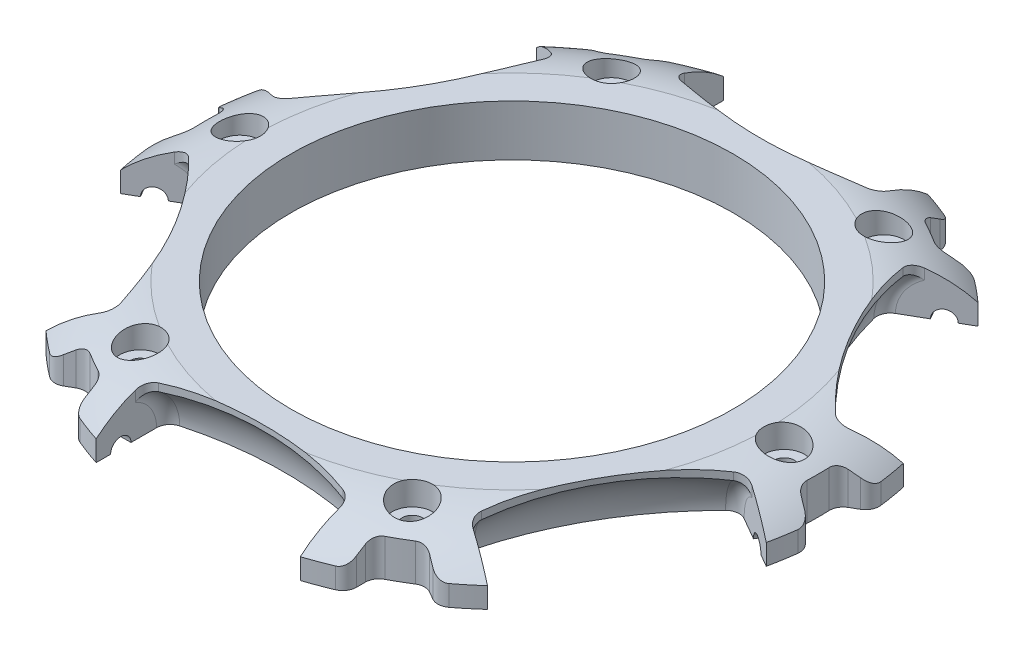
SolidWorks part; units mm, degrees
ref_plane "Front Plane" through (0, 0, 0) normal (0, 0, 1) x (1, 0, 0)
ref_plane "Top Plane" through (0, 0, 0) normal (0, 1, 0) x (1, 0, 0)
ref_plane "Right Plane" through (0, 0, 0) normal (1, 0, 0) x (0, 0, -1)
sketch "Sketch1" plane through (0, 0, 0) normal (0, 1, 0) x (1, 0, 0)
  line L10 (0, 0) -> (0, -50) construction
  line L11 (15, -42.5) -> (-15, -42.5) construction
  line L12 (15, -37.303) -> (15, -47.697)
  line L13 (-15, -37.303) -> (-15, -47.697)
  line L14 (-24.8054, -31.6419) -> (-33.8068, -36.8389)
  line L15 (-39.8054, -5.6611) -> (-48.8068, -10.8581)
  line L16 (-29.3061, -34.2404) -> (-44.3061, -8.2596) construction
  line L17 (-39.8054, 5.6611) -> (-48.8068, 10.8581)
  line L18 (-24.8054, 31.6419) -> (-33.8068, 36.8389)
  line L19 (-44.3061, 8.2596) -> (-29.3061, 34.2404) construction
  line L20 (-15, 37.303) -> (-15, 47.697)
  line L21 (15, 37.303) -> (15, 47.697)
  line L22 (-15, 42.5) -> (15, 42.5) construction
  line L23 (24.8054, 31.6419) -> (33.8068, 36.8389)
  line L24 (39.8054, 5.6611) -> (48.8068, 10.8581)
  line L25 (29.3061, 34.2404) -> (44.3061, 8.2596) construction
  line L26 (39.8054, -5.6611) -> (48.8068, -10.8581)
  line L27 (24.8054, -31.6419) -> (33.8068, -36.8389)
  line L28 (44.3061, -8.2596) -> (29.3061, -34.2404) construction
  line L103 (-16.5, -36.2148) -> (-16.5, -47.697)
  line L104 (16.5, -36.2148) -> (16.5, -47.697)
  circle A3 centre (0, 0) radius 50
  circle A4 centre (0, 0) radius 42.5 construction
  arc A8 (-15, -37.303) -> (15, -37.303) centre (0, -85) cw
  arc A9 (-39.8054, -5.6611) -> (-24.8054, -31.6419) centre (-73.6122, -42.5) cw
  arc A10 (-24.8054, 31.6419) -> (-39.8054, 5.6611) centre (-73.6122, 42.5) cw
  arc A11 (15, 37.303) -> (-15, 37.303) centre (0, 85) cw
  arc A12 (39.8054, 5.6611) -> (24.8054, 31.6419) centre (73.6122, 42.5) cw
  arc A13 (24.8054, -31.6419) -> (39.8054, -5.6611) centre (73.6122, -42.5) cw
  circle A38 centre (0, 0) radius 33.5
  circle A39 centre (0, 0) radius 28
  arc A40 (-16.5, -36.2148) -> (16.5, -36.2148) centre (0, -85) cw
  circle A41 centre (0, 0) radius 31
  point P18 (0, -42.5)
  point P28 (-36.8061, -21.25)
  point P36 (-36.8061, 21.25)
  point P44 (0, 42.5)
  point P52 (36.8061, 21.25)
  point P60 (36.8061, -21.25)
  point P65 (0, 0)
  dimension "D1" = 30
  dimension "D2" = 100
  dimension "D3" = 85
  dimension "D4" = 6
  dimension "D5" = 1.5
  dimension "D6" = 2.5
  dimension "D7" = 3
sketch "Sketch2" plane through (0, 0, 0) normal (0, 1, 0) x (1, 0, 0)
  circle A0 centre (0, 0) radius 50 construction
  circle A1 centre (0, 0) radius 50
extrude "Boss-Extrude1" add sketch "Sketch2" along normal blind 7.5
sketch "Sketch3" plane through (0, 0, 0) normal (0, 1, 0) x (1, 0, 0)
  line L5 (-20.18, -42.5) -> (20.5663, -42.5) construction
  line L6 (-15, -42.5) -> (15, -42.5)
  line L7 (-15, -42.5) -> (-15, -35.7329)
  line L8 (15, -42.5) -> (15, -35.7329)
  arc A0 (16.5, -36.2148) -> (-16.5, -36.2148) centre (0, -85) ccw construction
  arc A1 (15, -35.7329) -> (-15, -35.7329) centre (0, -85) ccw
revolve "Cut-Revolve1" cut sketch "Sketch3" angle 360 about L5
sketch "Sketch4" plane through (0, 0, 0) normal (0, 1, 0) x (1, 0, 0)
  line L5 (15, -38.8779) -> (15, -47.697)
  line L6 (-15, -37.303) -> (-15, -47.697) construction
  line L7 (-15, -38.8779) -> (-15, -47.697)
  arc A0 (16.5, -36.2148) -> (-16.5, -36.2148) centre (0, -85) ccw construction
  arc A1 (16.5, -36.2148) -> (-16.5, -36.2148) centre (0, -85) ccw construction
  arc A2 (15, -38.8779) -> (-15, -38.8779) centre (0, -85) ccw
  circle A3 centre (0, 0) radius 50 construction
  arc A4 (-15, -47.697) -> (15, -47.697) centre (0, 0) ccw
  dimension "D1" = 3
extrude "Cut-Extrude2" cut sketch "Sketch4" along normal up to next (7.5 mm away)
sketch "Sketch5" plane through (0, 0, 0) normal (1, 0, 0) x (0, 0, -1)
  circle A0 centre (-42.5, 0) radius 1.5
  point P0 (-42.5, 0)
  dimension "D1" = 3
extrude "Cut-Extrude3" cut sketch "Sketch5" against normal blind 18 and the other way blind 18
pattern_circular "CirPattern1" count 6 over 360 about axis through (0, 0, 0) along (0, 1, 0) of "Cut-Revolve1", "Cut-Extrude2", "Cut-Extrude3"
sketch "Sketch6" plane through (0, 0, 0) normal (0, -1, 0) x (1, 0, 0)
  line L0 (-29.1051, 37.5885) -> (-26.507, 36.0885) construction
  line L1 (-18, 44) -> (-18, 41) construction
  line L2 (-29.1051, 37.5885) -> (-26.507, 36.0885) construction
  line L3 (-18, 44) -> (-18, 41) construction
  line L4 (-20, 44) -> (-20, 41) construction
  line L5 (-28.1051, 39.3205) -> (-25.507, 37.8205) construction
  line L6 (-28.2647, 39.4126) -> (-24.9106, 37.4762)
  line L7 (-20, 40.3113) -> (-20, 44.1843)
  line L8 (20, 44.1843) -> (20, 40.3113)
  line L9 (24.9106, 37.4762) -> (28.2647, 39.4126)
  line L10 (48.2647, 4.7716) -> (44.9106, 2.8351)
  line L11 (44.9106, -2.8351) -> (48.2647, -4.7716)
  line L12 (28.2647, -39.4126) -> (24.9106, -37.4762)
  line L13 (20, -40.3113) -> (20, -44.1843)
  line L14 (-20, -44.1843) -> (-20, -40.3113)
  line L15 (-24.9106, -37.4762) -> (-28.2647, -39.4126)
  line L16 (-48.2647, -4.7716) -> (-44.9106, -2.8351)
  line L17 (-44.9106, 2.8351) -> (-48.2647, 4.7716)
  circle A1 centre (0, 0) radius 50 construction
  arc A4 (-20, 40.3113) -> (-24.9106, 37.4762) centre (0, 0) ccw
  arc A5 (-28.2647, 39.4126) -> (-48.2647, 4.7716) centre (0, 0) ccw
  arc A6 (24.9106, 37.4762) -> (20, 40.3113) centre (0, 0) ccw
  circle A7 centre (0, 0) radius 50
  arc A10 (44.9106, -2.8351) -> (44.9106, 2.8351) centre (0, 0) ccw
  arc A12 (20, -40.3113) -> (24.9106, -37.4762) centre (0, 0) ccw
  arc A14 (-24.9106, -37.4762) -> (-20, -40.3113) centre (0, 0) ccw
  arc A16 (-44.9106, 2.8351) -> (-44.9106, -2.8351) centre (0, 0) ccw
  arc A18 (20, 44.1843) -> (-20, 44.1843) centre (0, 0) ccw
  arc A19 (48.2647, 4.7716) -> (28.2647, 39.4126) centre (0, 0) ccw
  arc A20 (28.2647, -39.4126) -> (48.2647, -4.7716) centre (0, 0) ccw
  arc A21 (-20, -44.1843) -> (20, -44.1843) centre (0, 0) ccw
  arc A22 (-48.2647, -4.7716) -> (-28.2647, -39.4126) centre (0, 0) ccw
  point P1 (48.5, 0)
  point P15 (43.0337, 13.1567)
  point P48 (0, 0)
  dimension "D5" = 6
  dimension "D3" = 2
  dimension "D4" = 2
extrude "Cut-Extrude4" cut sketch "Sketch6" against normal up to next
sketch "Sketch8" plane through (0, 0, 0) normal (0, -1, 0) x (1, 0, 0)
  circle A2 centre (0, 0) radius 32.5
  circle A3 centre (0, 0) radius 32.5
  dimension "D1" = 1
extrude "Cut-Extrude5" cut sketch "Sketch8" against normal up to next
sketch "Sketch9" plane through (0, 0, 0) normal (0, -1, 0) x (1, 0, 0)
  line L0 (0, 0) -> (32.5, 0) construction
  line L1 (32.5, 0) -> (40, 0) construction
  circle A0 centre (0, 0) radius 32.5 construction
  circle A1 centre (40, 0) radius 1.5
  dimension "D2" = 3
  dimension "D1" = 40
extrude "Cut-Extrude6" cut sketch "Sketch9" against normal up to next (7.5 mm away)
sketch "Sketch10" plane through (0, 7.5, 0) normal (0, 1, 0) x (1, 0, 0)
  circle A0 centre (40, 0) radius 3
extrude "Cut-Extrude7" cut sketch "Sketch10" against normal offset from surface (3.5 mm away) 4 up to face at (40, 0, -1.5)
pattern_circular "CirPattern2" count 6 over 360 about axis through (0, 0, 0) along (0, 1, 0) of "Cut-Extrude7", "Cut-Extrude6"
sketch "Sketch7" plane through (0, 0, 0) normal (0, 0, 1) x (1, 0, 0)
  line L0 (-50, 0) -> (-50, 1.5) construction
  line L1 (50, 0) -> (-50, 0) construction
  line L2 (-26.1692, 7.5) -> (-41.1692, 7.5) construction
  line L3 (-37.542, 7.5) -> (-50, 7.5)
  line L4 (-50, 7.5) -> (-50, 1.5)
  line L5 (0, 0) -> (0, 7.5) construction
  line L6 (15, 7.5) -> (-15, 7.5) construction
  spline S0 degree 2 poles (-50, 1.5) (-45.2094, 6.974) (-37.542, 7.5) knots 0 0 0 1 1 1
revolve "Cut-Revolve2" cut sketch "Sketch7" angle 360 about L5
fillet "Fillet1" radius 2 12 edges at (-44.9106, 2.7403, -2.8351) (-44.9106, 2.7403, 2.8351) (-20, 2.7403, -40.3113) (-24.9106, 2.7403, -37.4762) (24.9106, 2.7403, -37.4762) (20, 2.7403, -40.3113) (44.9106, 2.7403, 2.8351) (44.9106, 2.7403, -2.8351) (24.9106, 2.7403, 37.4762) (20, 2.7403, 40.3113) (-20, 2.7403, 40.3113) (-24.9106, 2.7403, 37.4762)
fillet "Fillet2" radius 2 24 edges at (24.1714, 3.2621, -31.2759) (26.1692, 6.2583, -32.4293) (39.1714, 3.2621, -5.2951) (41.1692, 6.2583, -6.4486) (39.1714, 3.2621, 5.2951) (41.1692, 6.2583, 6.4486) (24.1714, 3.2621, 31.2759) (26.1692, 6.2583, 32.4293) (15, 6.2583, 38.8779) (15, 3.2621, 36.571) (-15, 3.2621, 36.571) (-15, 6.2583, 38.8779) (-26.1692, 6.2583, 32.4293) (-24.1714, 3.2621, 31.2759) (-41.1692, 6.2583, 6.4486) (-39.1714, 3.2621, 5.2951) (-41.1692, 6.2583, -6.4486) (-39.1714, 3.2621, -5.2951) (-26.1692, 6.2583, -32.4293) (-24.1714, 3.2621, -31.2759) (-15, 6.2583, -38.8779) (-15, 3.2621, -36.571) (15, 3.2621, -36.571) (15, 6.2583, -38.8779)
fillet "Fillet3" radius 2 12 edges at (-48.2647, 1.5146, 4.7716) (-48.2647, 1.5146, -4.7716) (-28.2647, 1.5146, -39.4126) (-20, 1.5146, -44.1843) (20, 1.5146, -44.1843) (28.2647, 1.5146, -39.4126) (48.2647, 1.5146, -4.7716) (48.2647, 1.5146, 4.7716) (20, 1.5146, 44.1843) (28.2647, 1.5146, 39.4126) (-28.2647, 1.5146, 39.4126) (-20, 1.5146, 44.1843)
